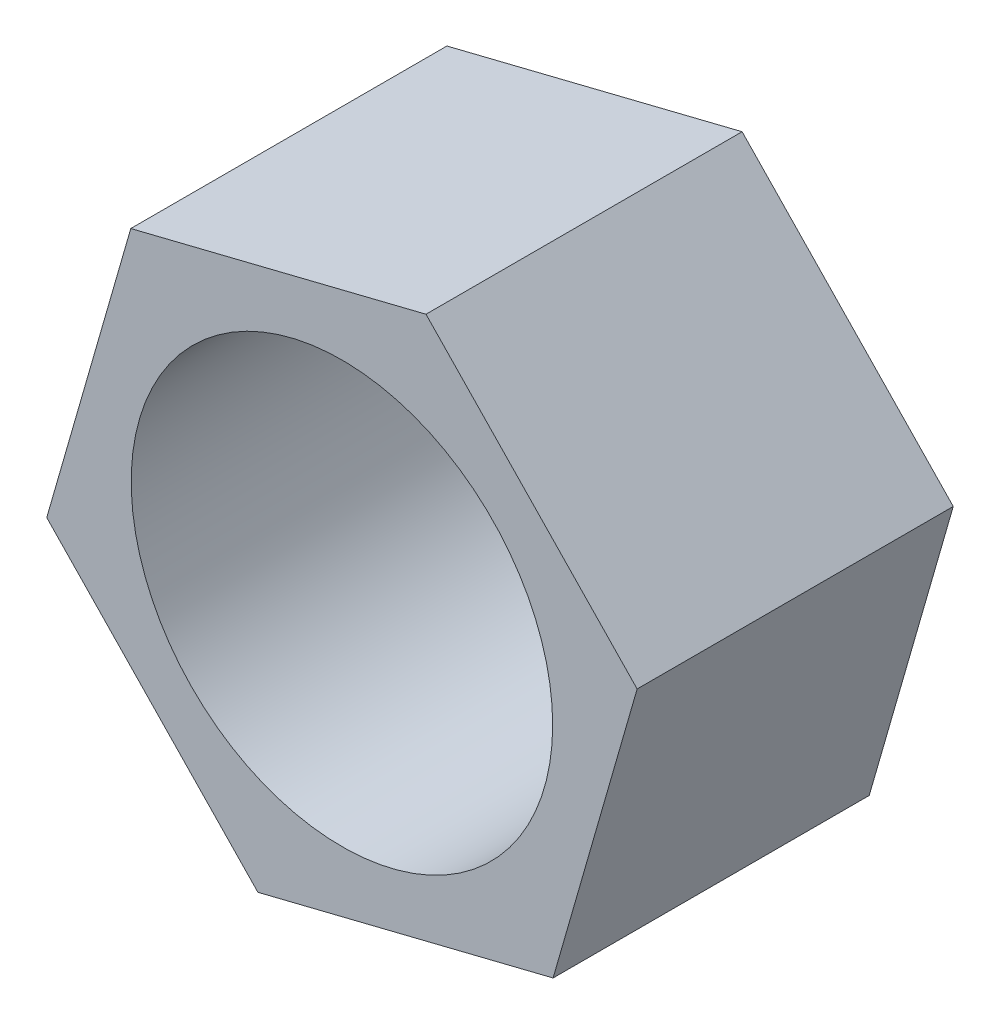
SolidWorks part; units mm, degrees
ref_plane "Front Plane" through (0, 0, 0) normal (0, 0, 1) x (1, 0, 0)
ref_plane "Top Plane" through (0, 0, 0) normal (0, 1, 0) x (1, 0, 0)
ref_plane "Right Plane" through (0, 0, 0) normal (1, 0, 0) x (0, 0, -1)
sketch "Sketch1" plane through (0, 0, 0) normal (0, 0, 1) x (1, 0, 0)
  line L1 (2.0038, -2.078) -> (2.8015, 0.6963)
  line L2 (2.8015, 0.6963) -> (0.7977, 2.7743)
  line L3 (0.7977, 2.7743) -> (-2.0038, 2.078)
  line L4 (-2.0038, 2.078) -> (-2.8015, -0.6963)
  line L5 (-2.8015, -0.6963) -> (-0.7977, -2.7743)
  line L6 (-0.7977, -2.7743) -> (2.0038, -2.078)
  circle A0 centre (0, 0) radius 2.5 construction
  circle A1 centre (0, 0) radius 2
  dimension "D1" = 5
  dimension "D2" = 4
extrude "Boss-Extrude1" add sketch "Sketch1" along normal blind 3
